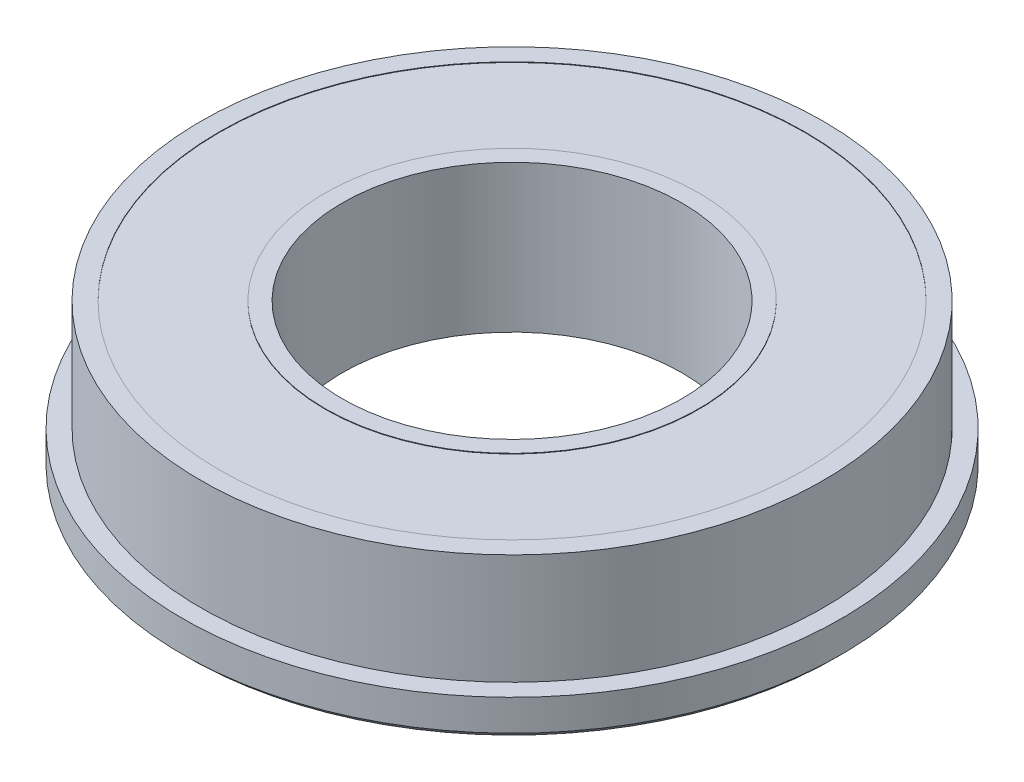
SolidWorks part; units mm, degrees
ref_plane "Front Plane" through (0, 0, 0) normal (0, 0, 1) x (1, 0, 0)
ref_plane "Top Plane" through (0, 0, 0) normal (0, 1, 0) x (1, 0, 0)
ref_plane "Right Plane" through (0, 0, 0) normal (1, 0, 0) x (0, 0, -1)
sketch "Sketch1" plane through (0, 0, 0) normal (0, 0, 1) x (1, 0, 0)
  line L0 (0, 0) -> (0, 16.1889) construction
  line L1 (15, 0) -> (16.5127, 0)
  line L2 (29.125, 0) -> (29.125, 3.25)
  line L3 (29.125, 3.25) -> (27.5, 3.25)
  line L4 (27.5, 3.25) -> (27.5, 13)
  line L5 (27.5, 13) -> (25.8734, 13)
  line L6 (15, 13) -> (15, 0)
  line L7 (16.5127, 13) -> (16.5127, 12.9516)
  line L8 (16.5127, 12.9516) -> (25.8734, 12.9516)
  line L9 (25.8734, 12.9516) -> (25.8734, 13)
  line L10 (15, 6.5) -> (19.0619, 6.5) construction
  line L11 (25.8734, 0.0484) -> (25.8734, 0)
  line L12 (16.5127, 0.0484) -> (25.8734, 0.0484)
  line L13 (16.5127, 0) -> (16.5127, 0.0484)
  line L14 (25.8734, 13) -> (16.5127, 13) construction
  line L15 (16.5127, 13) -> (15, 13)
  line L16 (16.5127, 0) -> (25.8734, 0) construction
  line L17 (25.8734, 0) -> (29.125, 0)
  dimension "D1" = 58.25
  dimension "D2" = 3.25
  dimension "D3" = 55
  dimension "D4" = 13
  dimension "D5" = 30
revolve "Revolve1" add sketch "Sketch1" angle 360 about L0
chamfer "Chamfer1" distance 0.5 angle 45 1 edges at (0, 0, -29.125)
